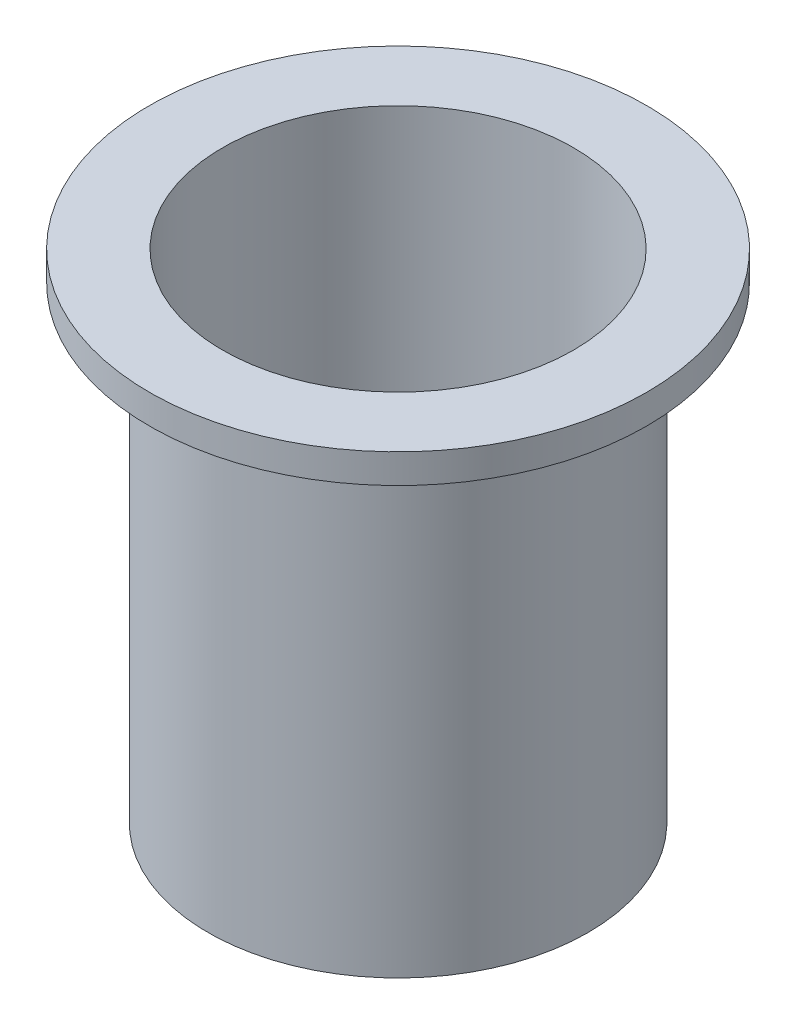
SolidWorks part; units mm, degrees
material "Delrin 2700 NC010, Low Viscosity Acetal Copolymer (SS)"
ref_plane "Front Plane" through (0, 0, 0) normal (0, 0, 1) x (1, 0, 0)
ref_plane "Top Plane" through (0, 0, 0) normal (0, 1, 0) x (1, 0, 0)
ref_plane "Right Plane" through (0, 0, 0) normal (1, 0, 0) x (0, 0, -1)
sketch "Sketch1" plane through (0, 0, 0) normal (0, 0, 1) x (1, 0, 0)
  line L0 (0, -554.3926) -> (0, 27165.2366) construction
  line L1 (41.275, 0) -> (30.744, 0)
  line L2 (41.275, 0) -> (41.275, 101.6)
  line L3 (38.1, 107.95) -> (41.275, 107.95)
  line L9 (38.1, 107.95) -> (38.1, 3.175)
  line L10 (41.275, 107.95) -> (53.975, 107.95)
  line L11 (30.744, 0) -> (0, 0)
  line L12 (41.275, 101.6) -> (53.975, 101.6)
  line L13 (53.975, 107.95) -> (53.975, 101.6)
  line L14 (0, 0) -> (0, 3.175)
  line L15 (0, 3.175) -> (38.1, 3.175)
  dimension "D1" = 76.2
  dimension "D2" = 3.175
  dimension "D4" = 3.175
  dimension "D5" = 98.425
  dimension "D8" = 6.35
  dimension "D9" = 12.7
revolve "Revolve1" add sketch "Sketch1" angle 360 about L0
